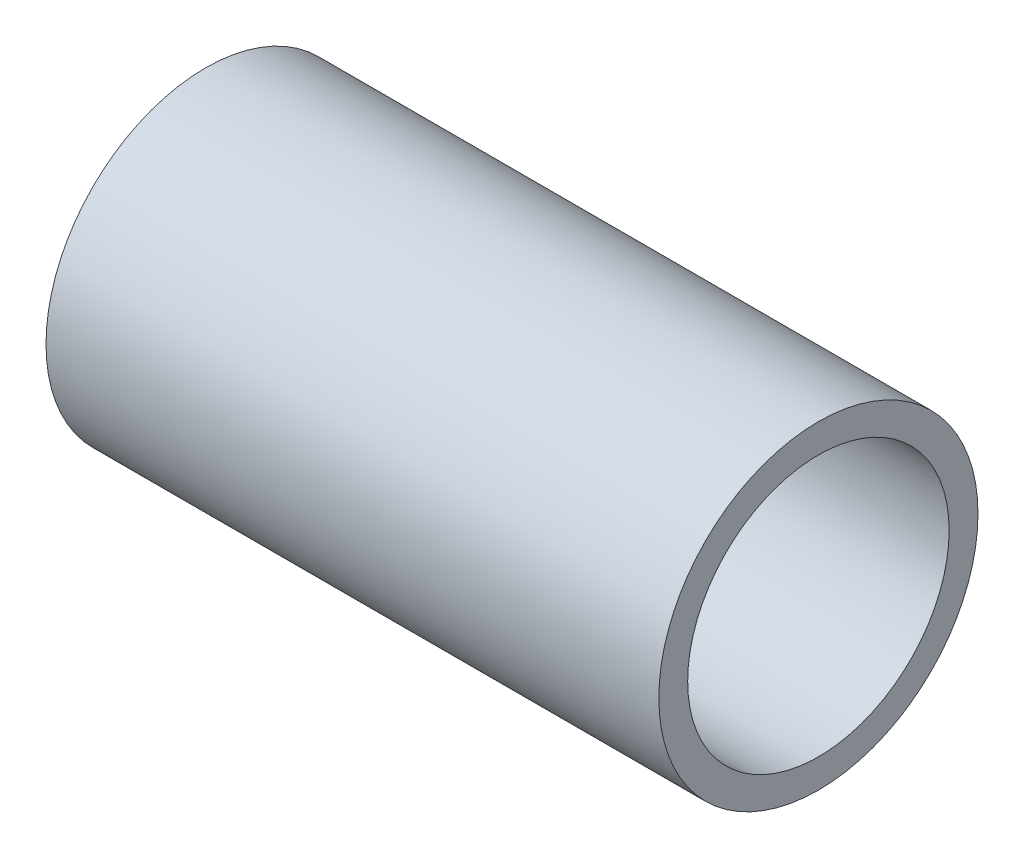
SolidWorks part; units mm, degrees
ref_plane "Front Plane" through (0, 0, 0) normal (0, 0, 1) x (1, 0, 0)
ref_plane "Top Plane" through (0, 0, 0) normal (0, 1, 0) x (1, 0, 0)
ref_plane "Right Plane" through (0, 0, 0) normal (1, 0, 0) x (0, 0, -1)
sketch "Sketch1" plane through (0, 0, 0) normal (1, 0, 0) x (0, 0, -1)
  circle A0 centre (0, 0) radius 1.6256
  circle A1 centre (0, 0) radius 1.9844
  dimension "D1" = 3.2512
  dimension "D2" = 3.9688
extrude "Boss-Extrude1" add sketch "Sketch1" along normal blind 7.62
